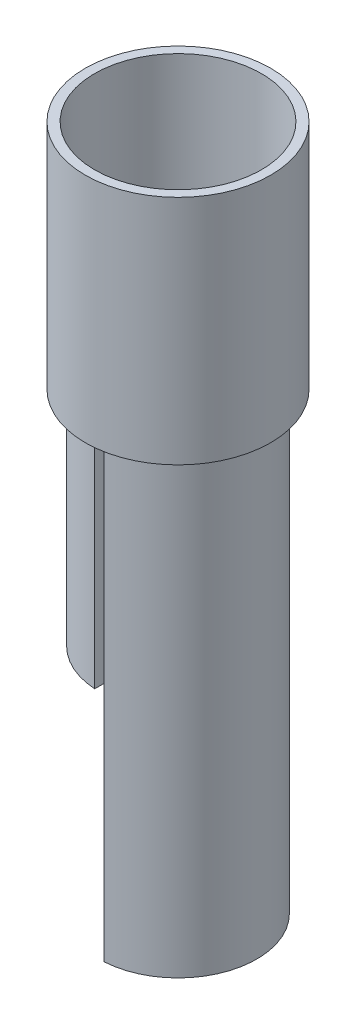
SolidWorks part; units mm, degrees
ref_plane "Front Plane" through (0, 0, 0) normal (0, 0, 1) x (1, 0, 0)
ref_plane "Top Plane" through (0, 0, 0) normal (0, 1, 0) x (1, 0, 0)
ref_plane "Right Plane" through (0, 0, 0) normal (1, 0, 0) x (0, 0, -1)
sketch "Sketch1" plane through (0, 0, 0) normal (0, 1, 0) x (1, 0, 0)
  circle A0 centre (0, 0) radius 20
  dimension "D1" = 40
extrude "Boss-Extrude1" add sketch "Sketch1" along normal blind 50
shell "Shell3" thickness 2
sketch "Sketch2" plane through (0, 2, 0) normal (0, 1, 0) x (1, 0, 0)
  line L0 (0, 18) -> (0, -18) construction
  line L1 (-1, 0) -> (1, 0) construction
  line L2 (-1, 16.9706) -> (-1, -16.9706)
  line L3 (1, 16.9706) -> (1, -16.9706)
  circle A0 centre (0, 0) radius 18 construction
  circle A1 centre (0, 0) radius 18 construction
  circle A2 centre (0, 0) radius 18
  circle A3 centre (0, 0) radius 17
  point P14 (0, 0)
  dimension "D1" = 36
  dimension "D2" = 34
  dimension "D3" = 1
extrude "Cut-Extrude1" cut sketch "Sketch2" against normal blind 50 contours L3 A3 | L2 A3
extrude "Boss-Extrude3" add sketch "Sketch2" against normal blind 50 separate body contours L3 A3 | L2 A3
shell "Shell6" thickness 2
shell "Shell7" thickness 2
sketch "Sketch7" plane through (0, -48, 0) normal (0, -1, 0) x (1, 0, 0)
  line L0 (1, 16.9706) -> (1, -16.9706)
  line L1 (3, 14.6969) -> (3, -14.6969)
  arc A0 (3, -14.6969) -> (3, 14.6969) centre (0, 0) ccw
  arc A2 (1, -16.9706) -> (1, 16.9706) centre (0, 0) ccw
extrude "processingadjust" add sketch "Sketch7" along normal blind 50
